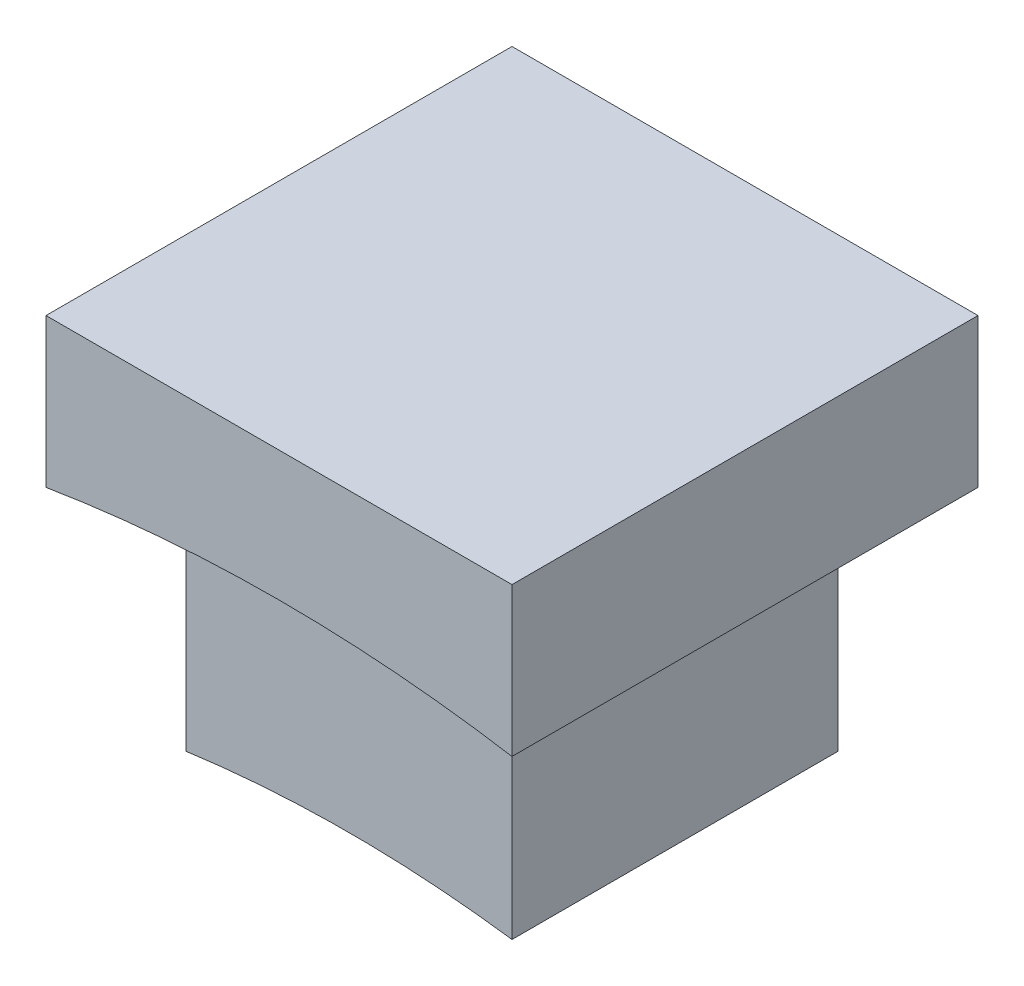
SolidWorks part; units mm, degrees
ref_plane "Front Plane" through (0, 0, 0) normal (0, 0, 1) x (1, 0, 0)
ref_plane "Top Plane" through (0, 0, 0) normal (0, 1, 0) x (1, 0, 0)
ref_plane "Right Plane" through (0, 0, 0) normal (1, 0, 0) x (0, 0, -1)
sketch "Sketch1" plane through (0, 0, 0) normal (0, 1, 0) x (1, 0, 0)
  line L1 (-7, -7) -> (7, -7)
  line L2 (-7, -7) -> (-7, 7)
  line L3 (-7, 7) -> (7, 7)
  line L4 (7, -7) -> (7, 7)
  line L5 (-7, -7) -> (7, 7) construction
  line L6 (-7, 7) -> (7, -7) construction
  point P3 (0, 0)
  dimension "D2" = 14
  dimension "D3" = 14
extrude "Boss-Extrude1" add sketch "Sketch1" along normal blind 10
sketch "Sketch2" plane through (0, 0, 0) normal (0, 0, 1) x (1, 0, 0)
  circle A0 centre (0, -37) radius 43.1
  dimension "D1" = 86.2
  dimension "D2" = 37
extrude "Cut-Extrude1" cut sketch "Sketch2" against normal through all both and the other way through all
sketch "Sketch3" plane through (0, 10, 0) normal (0, 1, 0) x (1, 0, 0)
  line L1 (-4.9, -4.9) -> (4.9, -4.9)
  line L2 (-4.9, -4.9) -> (-4.9, 4.9)
  line L3 (-4.9, 4.9) -> (4.9, 4.9)
  line L4 (4.9, -4.9) -> (4.9, 4.9)
  line L5 (-4.9, -4.9) -> (4.9, 4.9) construction
  line L6 (-4.9, 4.9) -> (4.9, -4.9) construction
  point P0 (0, 0)
  dimension "D2" = 9.8
  dimension "D3" = 9.8
extrude "Boss-Extrude2" add sketch "Sketch3" against normal blind 15
sketch "Sketch5" plane through (0, 0, 0) normal (0, 0, 1) x (1, 0, 0)
  circle A0 centre (0, -37) radius 36
  dimension "D1" = 72
  dimension "D2" = 37
extrude "Cut-Extrude2" cut sketch "Sketch5" against normal through all both and the other way through all
